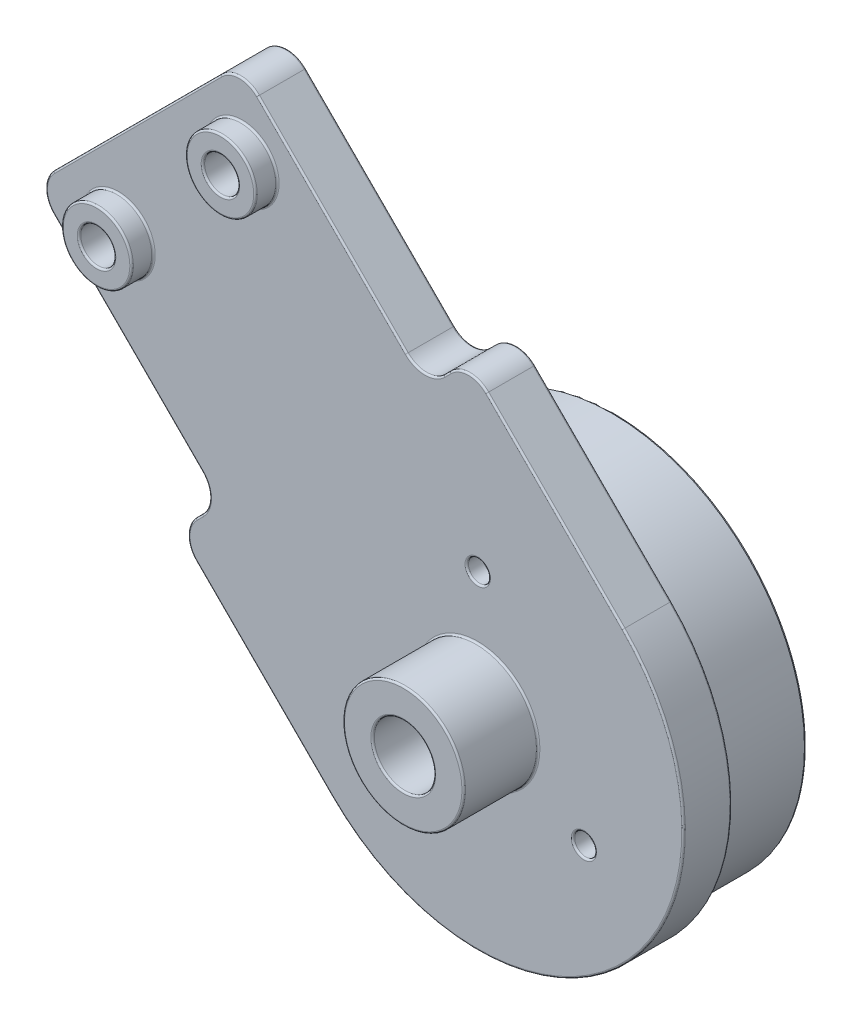
SolidWorks part; units mm, degrees
ref_plane "Front Plane" through (0, 0, 0) normal (0, 0, 1) x (1, 0, 0)
ref_plane "Top Plane" through (0, 0, 0) normal (0, 1, 0) x (1, 0, 0)
ref_plane "Right Plane" through (0, 0, 0) normal (1, 0, 0) x (0, 0, -1)
sketch "Sketch1" plane through (0, 0, 0) normal (0, 0, 1) x (1, 0, 0)
  line L0 (100, 0) -> (-100, 0)
  line L3 (-100, 0) -> (0, 100) construction
  line L4 (0, 100) -> (100, 0) construction
  line L5 (0, 0) -> (-50, 50) construction
  line L7 (0, 100) -> (0, 60) construction
  line L9 (-40, 60) -> (40, 60) construction
  circle A0 centre (-100, 0) radius 20
  circle A1 centre (0, 0) radius 20
  circle A2 centre (100, 0) radius 19.9987
  point P4 (0, 0)
  point P13 (0, 0)
  dimension "D5" = 40
  dimension "D6" = 39.9975
  dimension "D1" = 200
  dimension "D2" = 90
  dimension "D3" = 90
  dimension "D4" = 80
  dimension "D7" = 141.4214
  dimension "D8" = 70.7107
sketch "Sketch2" plane through (0, 0, 0) normal (0, 0, 1) x (1, 0, 0)
  line L0 (-56.5165, 43.4835) -> (-40, 60) construction
  line L1 (-100, 0) -> (0, 100) construction
  line L2 (-40, 60) -> (40, 60) construction
  line L3 (40, 60) -> (86.565, 13.435) construction
  line L4 (0, 100) -> (100, 0) construction
  line L5 (-49.4454, 36.4124) -> (-35.8579, 50)
  line L6 (-35.8579, 50) -> (35.8579, 50)
  line L7 (35.8579, 50) -> (79.4939, 6.364)
  line L8 (-63.5876, 50.5546) -> (-44.1421, 70)
  line L9 (-44.1421, 70) -> (44.1421, 70)
  line L10 (44.1421, 70) -> (93.636, 20.5061)
  line L11 (-63.5876, 50.5546) -> (-49.4454, 36.4124)
  line L12 (93.636, 20.5061) -> (79.4939, 6.364)
  line L13 (81.9688, 8.8388) -> (95.4038, -4.5962)
  line L14 (91.1612, 18.0312) -> (104.5962, 4.5962)
  line L15 (90.1005, 24.0416) -> (75.9584, 9.8995) construction
  line L16 (0, 100) -> (0, 60) construction
  line L17 (-6, 70) -> (-3.4486, 84.7178)
  line L18 (6, 70) -> (3.4486, 84.7178)
  circle A0 centre (100, 0) radius 3.5
  circle A1 centre (100, 0) radius 10 construction
  circle A3 centre (79.4939, 13.435) radius 1
  circle A4 centre (86.565, 20.5061) radius 1
  circle A5 centre (0, 60) radius 1.5
  circle A6 centre (0, 84.12) radius 1.5
  circle A8 centre (-50, 50) radius 1.5
  arc A9 (104.5962, 4.5962) -> (95.4038, -4.5962) centre (100, 0) cw
  arc A10 (-3.4486, 84.7178) -> (3.4486, 84.7178) centre (0, 84.12) cw
  point P51 (0, 70)
  dimension "D4" = 20
  dimension "D5" = 7
  dimension "D9" = 2
  dimension "D12" = 3
  dimension "D17" = 3
  dimension "D6" = 3
  dimension "D19" = 6.5
  dimension "D14" = 2
  dimension "D20" = 3.5
  dimension "D3" = 27.5
  dimension "D7" = 19
  dimension "D8" = 5
  dimension "D10" = 5
  dimension "D11" = 5
  dimension "D13" = 14.12
  dimension "D15" = 6
  dimension "D16" = 6
  dimension "D18" = 19
  dimension "D1" = 10
  dimension "D2" = 10
sketch "Sketch3" plane through (0, 0, 0) normal (0, 0, 1) x (1, 0, 0)
  line L0 (-86.565, 13.435) -> (-50, 50) construction
  line L1 (-100, 0) -> (0, 100) construction
  line L2 (-50, 50) -> (-13.435, 13.435) construction
  line L3 (0, 0) -> (-50, 50) construction
  line L4 (-79.4939, 6.364) -> (-50, 35.8579)
  line L5 (-50, 35.8579) -> (-20.5061, 6.364)
  line L6 (-93.636, 20.5061) -> (-50, 64.1421)
  line L7 (-50, 64.1421) -> (-6.364, 20.5061)
  line L8 (-93.636, 20.5061) -> (-79.4939, 6.364) construction
  line L9 (-20.5061, 6.364) -> (-6.364, 20.5061)
  line L10 (-91.1612, 18.0312) -> (-104.5962, 4.5962)
  line L11 (-81.9688, 8.8388) -> (-95.4038, -4.5962)
  line L12 (-18.0312, 8.8388) -> (-4.5962, -4.5962)
  line L13 (-8.8388, 18.0312) -> (4.5962, 4.5962)
  line L14 (-90.1005, 24.0416) -> (-75.9584, 9.8995)
  line L15 (-9.8995, 24.0416) -> (-24.0416, 9.8995)
  circle A0 centre (-100, 0) radius 10 construction
  circle A1 centre (-100, 0) radius 3.5
  circle A2 centre (0, 0) radius 10 construction
  circle A3 centre (0, 0) radius 3.5
  circle A6 centre (-86.565, 20.5061) radius 1
  circle A7 centre (-79.4939, 13.435) radius 1
  circle A8 centre (-13.435, 20.5061) radius 1
  circle A9 centre (-20.5061, 13.435) radius 1
  circle A10 centre (-50, 50) radius 1.5 construction
  circle A11 centre (-50, 50) radius 1.5
  arc A12 (4.5962, 4.5962) -> (-4.5962, -4.5962) centre (0, 0) cw
  arc A13 (-104.5962, 4.5962) -> (-95.4038, -4.5962) centre (-100, 0) ccw
  dimension "D1" = 20
  dimension "D2" = 7
  dimension "D9" = 2
  dimension "D13" = 2
  dimension "D16" = 6.5
  dimension "D18" = 3
  dimension "D3" = 6.5
  dimension "D19" = 3
  dimension "D6" = 19
  dimension "D7" = 19
  dimension "D8" = 5
  dimension "D10" = 5
  dimension "D11" = 5
  dimension "D12" = 5
  dimension "D14" = 5
  dimension "D15" = 5
  dimension "D17" = 13.435
  dimension "D4" = 10
  dimension "D5" = 10
sketch "Sketch4" plane through (0, 0, 0) normal (0, 0, 1) x (1, 0, 0)
  line L6 (-57.5, 92.6154) -> (57.5, 92.6154)
  line L7 (57.5, 92.6154) -> (57.5, 82.6154)
  line L8 (57.5, 82.6154) -> (44.1421, 70)
  line L9 (44.1421, 70) -> (-44.1421, 70)
  line L10 (-44.1421, 70) -> (-57.5, 82.6154)
  line L11 (-57.5, 82.6154) -> (-57.5, 92.6154)
  line L12 (-4, 60) -> (-4, 70)
  line L13 (4, 60) -> (4, 70)
  line L14 (-22.5, 84.1154) -> (22.5, 84.1154) construction
  line L15 (-22.5, 88.6154) -> (22.5, 88.6154)
  line L16 (-22.5, 79.6154) -> (22.5, 79.6154)
  arc A0 (-4, 60) -> (4, 60) centre (0, 60) ccw
  arc A1 (-22.5, 88.6154) -> (-22.5, 79.6154) centre (-22.5, 84.1154) ccw
  circle A2 centre (0, 60) radius 1.5 construction
  arc A4 (22.5, 79.6154) -> (22.5, 88.6154) centre (22.5, 84.1154) ccw
  point P2 (0, 92.6154)
  point P15 (0, 84.1154)
  dimension "D3" = 4
  dimension "D8" = 2.5
  dimension "D1" = 115
  dimension "D2" = 10
  dimension "D4" = 45
  dimension "D5" = 9
  dimension "D6" = 12.6154
  dimension "D7" = 4
sketch "Sketch6" plane through (0, 0, 0) normal (0, 0, 1) x (1, 0, 0)
  line L0 (74.7209, 13.6118) -> (86.3882, 25.2791)
  line L1 (0, 100) -> (100, 0) construction
  line L2 (90.1005, 24.0416) -> (75.9584, 9.8995) construction
  line L3 (74.7209, 13.6118) -> (85.3275, 3.0052)
  line L4 (85.3275, 3.0052) -> (82.8527, 0.5303)
  line L5 (82.8527, 0.5303) -> (91.6915, -8.3085)
  line L6 (100, 0) -> (90.078, 9.922) construction
  line L7 (99.4697, 17.1473) -> (108.3085, 8.3085)
  line L8 (96.9948, 14.6725) -> (99.4697, 17.1473)
  line L9 (86.3882, 25.2791) -> (96.9948, 14.6725)
  circle A0 centre (100, 0) radius 10 construction
  circle A1 centre (100, 0) radius 10
  arc A3 (91.6915, -8.3085) -> (108.3085, 8.3085) centre (100, 0) ccw
  circle A4 centre (86.565, 20.5061) radius 1 construction
  circle A5 centre (79.4939, 13.435) radius 1 construction
  circle A6 centre (86.565, 20.5061) radius 1
  circle A7 centre (79.4939, 13.435) radius 1
  point P7 (80.5546, 19.4454)
  point P24 (0, 0)
  point P25 (0, 0)
  point P26 (0, 0)
  dimension "D1" = 11.75
  dimension "D5" = 1.75
  dimension "D2" = 16.5
  dimension "D3" = 15
  dimension "D4" = 12.5
extrude "Boss-Extrude1" add sketch "Sketch6" along normal blind 2.75
sketch "Sketch7" plane through (0, 0, 2.75) normal (0, 0, 1) x (1, 0, 0)
  circle A0 centre (100, 0) radius 10 construction
  circle A1 centre (100, 0) radius 10
extrude "Boss-Extrude2" add sketch "Sketch7" against normal blind 1
sketch "Sketch8" plane through (0, 0, 0) normal (0, 0, -1) x (-1, 0, 0)
  circle A1 centre (-100, 0) radius 10
  circle A2 centre (-100, 0) radius 10
  circle A4 centre (-100, 0) radius 11
  circle A5 centre (-100, 0) radius 11
  dimension "D1" = 0
  dimension "D2" = 1
extrude "Boss-Extrude3" add sketch "Sketch8" along normal blind 5
fillet "Fillet1" radius 1.5 6 edges at (74.7209, 13.6118, 1.375) (96.9948, 14.6725, 1.375) (99.4697, 17.1473, 1.375) (82.8527, 0.5303, 1.375) (85.3275, 3.0052, 1.375) (86.3882, 25.2791, 1.375)
sketch "Sketch9" plane through (0, 0, 2.75) normal (0, 0, 1) x (1, 0, 0)
  circle A0 centre (79.4939, 13.435) radius 1 construction
  circle A1 centre (86.565, 20.5061) radius 1 construction
  circle A2 centre (79.4939, 13.435) radius 1
  circle A3 centre (86.565, 20.5061) radius 1
  circle A4 centre (79.4939, 13.435) radius 2
  circle A5 centre (86.565, 20.5061) radius 2
  dimension "D1" = 1
extrude "Boss-Extrude4" add sketch "Sketch9" along normal blind 1.25
sketch "Sketch12" plane through (0, 0, 2.75) normal (0, 0, 1) x (1, 0, 0)
  circle A0 centre (100, 0) radius 1.75
  dimension "D1" = 3.5
extrude "Cut-Extrude1" cut sketch "Sketch12" against normal up to surface (1 mm away) up to face at (110, 0, 1.75)
sketch "Sketch13" plane through (0, 0, 2.75) normal (0, 0, 1) x (1, 0, 0)
  circle A0 centre (100, 0) radius 3.45
  circle A2 centre (100, 0) radius 1.75 construction
  circle A3 centre (100, 0) radius 1.75
  dimension "D1" = 6.9
extrude "Boss-Extrude6" add sketch "Sketch13" along normal blind 4.25
sketch "Sketch14" plane through (0, 0, 2.75) normal (0, 0, 1) x (1, 0, 0)
  line L0 (100, 0) -> (100, 7) construction
  circle A0 centre (100, 7) radius 0.625
  circle A1 centre (106.0622, -3.5) radius 0.625
  circle A2 centre (93.9378, -3.5) radius 0.625
  point P11 (100, 0)
  dimension "D1" = 1.25
  dimension "D2" = 7
  dimension "D3" = 3
extrude "Cut-Extrude2" cut sketch "Sketch14" against normal up to surface (1 mm away) up to face at (101.75, 0, 1.75)
fillet "Fillet3" radius 0.1 50 edges at (94.5628, -3.5, 2.75) (94.5628, -3.5, 1.75) (106.6872, -3.5, 2.75) (106.6872, -3.5, 1.75) (100.625, 7, 2.75) (100.625, 7, 1.75) (101.75, 0, 7) (103.45, 0, 2.75) (103.45, 0, 7) (101.75, 0, 1.75) (87.565, 20.5061, 4) (88.565, 20.5061, 2.75) (88.565, 20.5061, 4) (80.4939, 13.435, 4) (81.4939, 13.435, 2.75) (81.4939, 13.435, 4) (90, 0, -5) (89, 0, -5) (110, 0, 1.75) (80.4939, 13.435, 0) (87.565, 20.5061, 0) (80.0242, 8.3085, 0) (84.0901, 1.7678, 0) (87.8024, -4.4194, 0) (108.3085, -8.3085, 0) (104.4194, 12.1976, 0) (98.2322, 15.9099, 0) (91.6915, 19.9758, 0) (80.5546, 19.4454, 0) (80.0242, 8.3085, 2.75) (84.0901, 1.7678, 2.75) (87.8024, -4.4194, 2.75) (108.3085, -8.3085, 2.75) (98.2322, 15.9099, 2.75) (91.6915, 19.9758, 2.75) (80.5546, 19.4454, 2.75) (111, 0, 0) (86.3882, 24.6577, 0) (83.474, 0.5303, 0) (99.4697, 16.526, 0) (75.3423, 13.6118, 0) (86.3882, 24.6577, 2.75) (83.474, 0.5303, 2.75) (99.4697, 16.526, 2.75) (75.3423, 13.6118, 2.75) (96.9948, 15.2938, 0) (96.9948, 15.2938, 2.75) (84.7062, 3.0052, 0) (84.7062, 3.0052, 2.75) (104.4194, 12.1976, 2.75)
